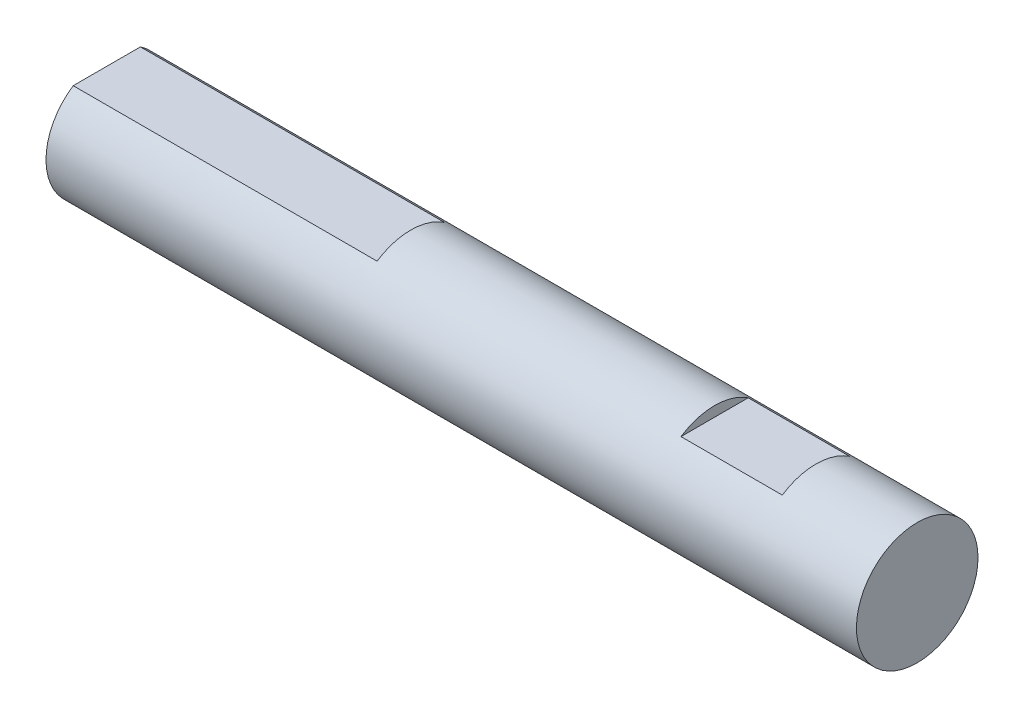
SolidWorks part; units mm, degrees
ref_plane "前视基准面" through (0, 0, 0) normal (0, 0, 1) x (1, 0, 0)
ref_plane "上视基准面" through (0, 0, 0) normal (0, 1, 0) x (1, 0, 0)
ref_plane "右视基准面" through (0, 0, 0) normal (1, 0, 0) x (0, 0, -1)
other "Configuration Table"
sketch "草图1" plane through (0, 0, 0) normal (1, 0, 0) x (0, 0, -1)
  circle A0 centre (0, 0) radius 6
extrude "凸台-拉伸1" add sketch "草图1" along normal blind 70
sketch "草图2" plane through (0, 0, 0) normal (0, 0, 1) x (1, 0, 0)
  line L0 (0, 6) -> (0, -6) construction
  line L1 (60, 6) -> (50, 6)
  line L3 (60, 5) -> (50, 5)
  line L4 (0, 6) -> (0, 5)
  line L5 (20, 6) -> (20, 5)
  line L6 (50, 6) -> (50, 5)
  line L7 (20, 6) -> (0, 6)
  line L8 (20, 5) -> (0, 5)
  line L9 (60, 6) -> (60, 5)
  point P11 (0, 5.5)
  dimension "D1" = 10
  dimension "D2" = 20
extrude "切除-拉伸1" cut sketch "草图2" against normal mid plane 70
sketch "草图3" plane through (0, 0, 0) normal (-1, 0, 0) x (0, 0, 1)
  line L0 (-3.3166, 5) -> (3.3166, 5) construction
  line L1 (-3.3166, 5) -> (3.3166, 5)
  arc A0 (-3.3166, 5) -> (3.3166, 5) centre (0, 0) ccw construction
  arc A1 (-3.3166, 5) -> (3.3166, 5) centre (0, 0) ccw
extrude "凸台-拉伸2" add sketch "草图3" along normal blind 10
